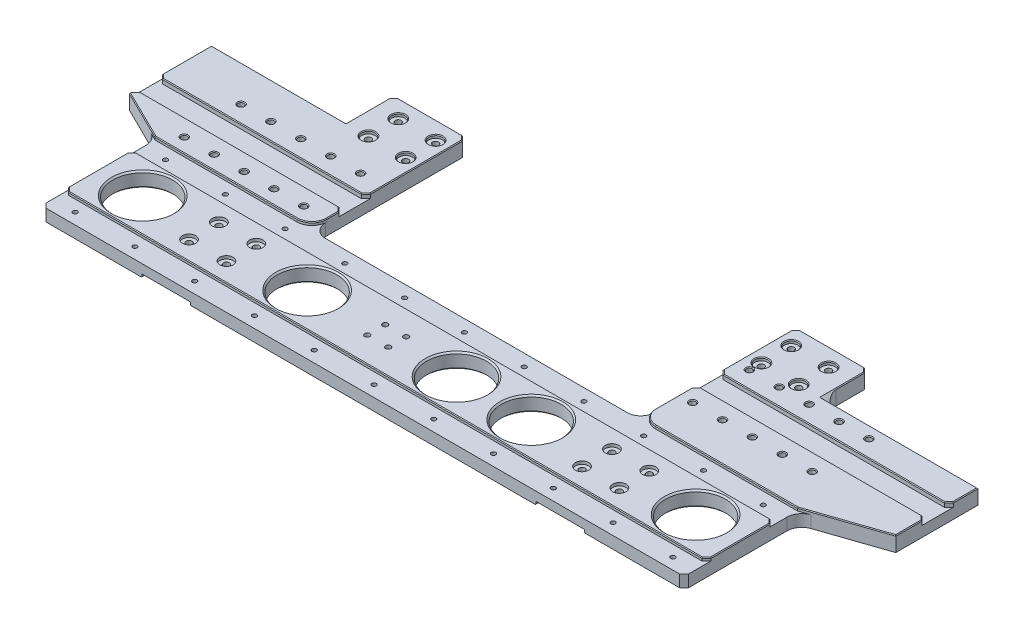
SolidWorks part; units mm, degrees
ref_plane "Front Plane" through (0, 0, 0) normal (0, 0, 1) x (1, 0, 0)
ref_plane "Top Plane" through (0, 0, 0) normal (0, 1, 0) x (1, 0, 0)
ref_plane "Right Plane" through (0, 0, 0) normal (1, 0, 0) x (0, 0, -1)
sketch "Sketch1" plane through (0, 0, 0) normal (0, 1, 0) x (1, 0, 0)
  line L0 (-110, 76) -> (110, 76)
  line L1 (0, -55) -> (0, 55) construction
  line L2 (110, 76) -> (110, 179.75)
  line L3 (110, 179.75) -> (159, 179.75)
  line L4 (159, 179.75) -> (159, 0)
  line L5 (-55, 0) -> (55, 0) construction
  line L6 (159, 0) -> (-159, 0)
  line L7 (-159, 179.75) -> (-159, 0)
  line L8 (-110, 179.75) -> (-159, 179.75)
  line L9 (-110, 76) -> (-110, 179.75)
  line L10 (-139.3864, 37.75) -> (-93.4466, 37.75) construction
  line L11 (-144, 47.75) -> (-119, 27.75) construction
  line L12 (-144, 167.75) -> (-119, 147.75) construction
  line L13 (-115.375, 179) -> (-147.625, 179) construction
  line L14 (-115.375, 179) -> (-115.375, 136.5) construction
  line L15 (-115.375, 136.5) -> (-147.625, 136.5) construction
  line L16 (-147.625, 179) -> (-147.625, 136.5) construction
  line L17 (-115.375, 179) -> (-147.625, 136.5) construction
  line L18 (-115.375, 136.5) -> (-147.625, 179) construction
  line L19 (119, 167.75) -> (144, 147.75) construction
  circle A0 centre (-119, 167.75) radius 2
  circle A1 centre (-144, 167.75) radius 2
  circle A2 centre (-144, 147.75) radius 2
  circle A3 centre (-119, 147.75) radius 2
  circle A4 centre (-119, 27.75) radius 2
  circle A5 centre (-119, 47.75) radius 2
  circle A6 centre (-144, 47.75) radius 2
  circle A7 centre (-144, 27.75) radius 2
  circle A8 centre (144, 167.75) radius 2
  circle A9 centre (119, 167.75) radius 2
  circle A10 centre (144, 147.75) radius 2
  circle A11 centre (119, 147.75) radius 2
  circle A12 centre (144, 27.75) radius 2
  circle A13 centre (144, 47.75) radius 2
  circle A14 centre (119, 47.75) radius 2
  circle A15 centre (119, 27.75) radius 2
  circle A16 centre (-20, 68) radius 2 construction
  circle A17 centre (-60, 68) radius 2 construction
  circle A18 centre (-100, 68) radius 2 construction
  circle A19 centre (-140, 68) radius 2 construction
  circle A20 centre (20, 68) radius 2 construction
  circle A21 centre (60, 68) radius 2 construction
  circle A22 centre (100, 68) radius 2 construction
  circle A23 centre (140, 68) radius 2 construction
  circle A24 centre (140, 7.5) radius 2 construction
  circle A25 centre (100, 7.5) radius 2 construction
  circle A26 centre (60, 7.5) radius 2 construction
  circle A27 centre (20, 7.5) radius 2 construction
  circle A28 centre (-20, 7.5) radius 2 construction
  circle A29 centre (-60, 7.5) radius 2 construction
  circle A30 centre (-100, 7.5) radius 2 construction
  circle A31 centre (-140, 7.5) radius 2 construction
  circle A32 centre (-25, 37.75) radius 20 construction
  circle A33 centre (-75, 37.75) radius 20
  circle A34 centre (75, 37.75) radius 20
  circle A35 centre (25, 37.75) radius 20
  circle A36 centre (-125, 123.55) radius 2
  circle A37 centre (-125, 85.55) radius 2
  circle A38 centre (119, 139.75) radius 2
  circle A39 centre (119, 101.75) radius 2
  point P12 (0, 0)
  point P15 (0, 76)
  point P49 (-131.5, 37.75)
  point P96 (-131.5, 157.75)
  point P103 (131.5, 157.75)
  dimension "D5" = 119
  dimension "D6" = 25
  dimension "D8" = 4
  dimension "D10" = 12
  dimension "D11" = 20
  dimension "D12" = 120
  dimension "D13" = 30.25
  dimension "D16" = 40
  dimension "D2" = 7.5
  dimension "D4" = 8
  dimension "D17" = 40
  dimension "D20" = 50
  dimension "D21" = 15
  dimension "D3" = 9
  dimension "D22" = 56.2
  dimension "D23" = 15
  dimension "D25" = 38
  dimension "D26" = 40
  dimension "D28" = 38
  dimension "D14" = 20
  dimension "D18" = 25
  dimension "D29" = 32.25
  dimension "D30" = 42.5
  dimension "D31" = 263
  dimension "D7" = 2
  dimension "D9" = 2
  dimension "D15" = 4
  dimension "D19" = 2
  dimension "D24" = 2
  dimension "D27" = 2
extrude "Boss-Extrude1" add sketch "Sketch1" along normal mid plane 6 contours L0 L9 L8 L7 L6 L4 L3 L2 A39 A38 A11 A37 A36 A34 A33 A32 A30 A28 A27 A26 A25 A24 A22 A20 A19 A18 A17 A16 A14 A12
sketch "Sketch2" plane through (0, -3, 0) normal (0, 1, 0) x (1, 0, 0)
  line L0 (-159, 179.75) -> (-159, 0) construction
  line L1 (-147.625, 0) -> (-159, 0)
  line L2 (-147.625, 0) -> (-147.625, 179.75)
  line L3 (-147.625, 179.75) -> (-159, 179.75)
  line L4 (-159, 0) -> (-159, 179.75)
  line L5 (-110, 179.75) -> (-159, 179.75) construction
  line L7 (159, 0) -> (-159, 0) construction
  line L8 (-147.625, 179) -> (-147.625, 136.5) construction
extrude "Boss-Extrude2" add sketch "Sketch2" against normal blind 2
sketch "Sketch6" plane through (0, 3, 0) normal (0, 1, 0) x (1, 0, 0)
  line L0 (-55, 0) -> (55, 0) construction
  line L1 (159, 0) -> (215, 0)
  line L2 (159, 0) -> (159, 76)
  line L3 (159, 76) -> (215, 76)
  line L4 (215, 0) -> (215, 76)
  line L5 (159, 179.75) -> (159, 0) construction
  line L6 (-110, 76) -> (110, 76) construction
  line L7 (0, 0) -> (0, 76) construction
  line L9 (-215, 0) -> (-215, 76)
  line L10 (-159, 76) -> (-215, 76)
  line L11 (-159, 0) -> (-159, 76)
  line L12 (-159, 0) -> (-215, 0)
  dimension "D1" = 215
extrude "Boss-Extrude5" add sketch "Sketch6" against normal up to surface (8 mm away) up to face at (-153.3125, -5, -89.875)
sketch "Sketch3" plane through (0, 3, 0) normal (0, 1, 0) x (1, 0, 0)
  line L0 (-159, 179.75) -> (-159, 0) construction
  line L1 (215, 15) -> (-215, 15)
  line L2 (215, 15) -> (215, 60.5)
  line L3 (215, 60.5) -> (-215, 60.5)
  line L4 (-215, 15) -> (-215, 60.5)
  line L5 (159, 179.75) -> (159, 0) construction
  line L6 (110, 179.75) -> (159, 179.75) construction
  line L7 (-110, 76) -> (-110, 179.75) construction
  line L8 (-159, 179.75) -> (-110, 179.75)
  line L9 (-159, 179.75) -> (-159, 76)
  line L10 (-159, 76) -> (-110, 76)
  line L11 (-110, 179.75) -> (-110, 76)
  line L12 (-110, 179.75) -> (-159, 179.75) construction
  line L13 (159, 0) -> (-159, 0) construction
  line L14 (110, 76) -> (110, 179.75) construction
  line L16 (110, 179.75) -> (159, 179.75)
  line L17 (110, 179.75) -> (110, 76)
  line L18 (110, 76) -> (159, 76)
  line L19 (159, 179.75) -> (159, 76)
  line L22 (215, 0) -> (215, 76) construction
  line L23 (-215, 76) -> (-215, 0) construction
  line L24 (-110, 76) -> (110, 76) construction
  line L25 (215, 76) -> (159, 76) construction
  circle A0 centre (-75, 37.75) radius 20
  circle A1 centre (-25, 37.75) radius 20 construction
  circle A2 centre (25, 37.75) radius 20
  circle A3 centre (75, 37.75) radius 20
  circle A4 centre (-75, 37.75) radius 20 construction
  circle A5 centre (-25, 37.75) radius 20 construction
  circle A6 centre (25, 37.75) radius 20 construction
  circle A7 centre (75, 37.75) radius 20 construction
  circle A8 centre (-144, 47.75) radius 4.45
  circle A9 centre (-119, 47.75) radius 4.45
  circle A10 centre (-144, 27.75) radius 4.45
  circle A11 centre (-119, 27.75) radius 4.45
  circle A12 centre (-144, 47.75) radius 2 construction
  circle A13 centre (-144, 167.75) radius 2 construction
  circle A14 centre (-119, 27.75) radius 2 construction
  circle A15 centre (-119, 47.75) radius 2 construction
  circle A16 centre (-144, 27.75) radius 2 construction
  circle A17 centre (119, 47.75) radius 4.45
  circle A18 centre (119, 27.75) radius 4.45
  circle A19 centre (144, 27.75) radius 4.45
  circle A20 centre (144, 47.75) radius 4.45
  circle A21 centre (-144, 167.75) radius 4.45
  circle A22 centre (119, 101.75) radius 2 construction
  circle A23 centre (-119, 167.75) radius 4.45
  circle A24 centre (-144, 147.75) radius 4.45
  circle A25 centre (-125, 123.55) radius 2
  circle A26 centre (-119, 147.75) radius 4.45
  circle A27 centre (-125, 85.55) radius 2
  circle A28 centre (119, 167.75) radius 4.45
  circle A29 centre (119, 139.75) radius 2
  circle A30 centre (119, 147.75) radius 4.45
  circle A31 centre (119, 101.75) radius 2
  circle A32 centre (144, 147.75) radius 4.45
  circle A33 centre (144, 167.75) radius 4.45
  circle A35 centre (-125, 123.55) radius 2 construction
  circle A36 centre (-125, 85.55) radius 2 construction
  circle A37 centre (119, 139.75) radius 2 construction
  dimension "D1" = 8.9
  dimension "D2" = 15
  dimension "D4" = 45.5
extrude "Boss-Extrude3" add sketch "Sketch3" along normal blind 2
sketch "Sketch4" plane through (0, -3, 0) normal (0, -1, 0) x (1, 0, 0)
  line L0 (110, -179.75) -> (110, -76)
  line L1 (110, -76) -> (-110, -76)
  line L2 (-110, -76) -> (-110, -179.75)
  line L3 (-110, -179.75) -> (-115.375, -179.75)
  line L4 (159, 0) -> (-147.625, 0) construction
  line L5 (-110, -76) -> (-110, -179.75) construction
  line L6 (-115.375, -179.75) -> (-115.375, 0)
  line L8 (-115.375, 0) -> (116, 0)
  line L9 (116, 0) -> (116, -179.75)
  line L11 (116, -179.75) -> (110, -179.75)
  line L12 (116, -183.9) -> (116, -131.6) construction
  line L14 (159, 0) -> (148.25, 0)
  line L15 (159, 0) -> (159, -179.75)
  line L16 (159, -179.75) -> (148.25, -179.75)
  line L17 (148.25, 0) -> (148.25, -179.75)
  line L19 (-110, -179.75) -> (-147.625, -179.75) construction
  line L20 (-110, -76) -> (110, -76) construction
  line L21 (110, -76) -> (110, -179.75) construction
  line L22 (110, -179.75) -> (159, -179.75) construction
  line L23 (159, -179.75) -> (159, 0) construction
  line L24 (-115.375, -179) -> (-115.375, -136.5) construction
  line L25 (-115.375, -136.5) -> (-147.625, -136.5) construction
  line L26 (-115.375, -136.5) -> (-147.625, -136.5) construction
  line L27 (0.3125, 0) -> (0.3125, -76.0006) construction
  line L28 (116, -136.5) -> (148.25, -136.5) construction
  circle A8 centre (-100, -68) radius 2
  circle A9 centre (-60, -68) radius 2
  circle A10 centre (-20, -68) radius 2
  circle A11 centre (20, -68) radius 2
  circle A12 centre (60, -68) radius 2
  circle A13 centre (100, -68) radius 2
  circle A14 centre (100, -7.5) radius 2
  circle A15 centre (60, -7.5) radius 2
  circle A16 centre (20, -7.5) radius 2
  circle A17 centre (-20, -7.5) radius 2
  circle A18 centre (-60, -7.5) radius 2
  circle A19 centre (-100, -7.5) radius 2
  circle A20 centre (-100, -7.5) radius 2 construction
  circle A21 centre (-60, -7.5) radius 2 construction
  circle A22 centre (-20, -7.5) radius 2 construction
  circle A23 centre (20, -7.5) radius 2 construction
  circle A24 centre (60, -7.5) radius 2 construction
  circle A25 centre (100, -7.5) radius 2 construction
  circle A26 centre (-100, -68) radius 2 construction
  circle A27 centre (-60, -68) radius 2 construction
  circle A28 centre (-20, -68) radius 2 construction
  circle A29 centre (20, -68) radius 2 construction
  circle A30 centre (60, -68) radius 2 construction
  circle A31 centre (100, -68) radius 2 construction
  circle A32 centre (-75, -37.75) radius 20 construction
  circle A34 centre (25, -37.75) radius 20 construction
  circle A35 centre (75, -37.75) radius 20 construction
  circle A36 centre (-75, -37.75) radius 20
  circle A38 centre (25, -37.75) radius 20
  circle A39 centre (75, -37.75) radius 20
extrude "Boss-Extrude4" add sketch "Sketch4" along normal blind 2
fillet "Fillet1" radius 10 2 edges at (-110, 4, -76) (110, 4, -76)
fillet "Fillet2" radius 9 2 edges at (110, -1, -76) (-110, -1, -76)
sketch "Sketch9" plane through (0, 3, 0) normal (0, 1, 0) x (1, 0, 0)
  line L0 (215, 60.5) -> (-215, 60.5) construction
  line L1 (-215, 76) -> (-215, 60.5) construction
  line L2 (-215, 15) -> (215, 15) construction
  circle A0 centre (-200, 68) radius 1.5
  circle A1 centre (-200, 7.5) radius 1.5
  circle A2 centre (-160, 7.5) radius 1.5
  circle A3 centre (-160, 68) radius 1.5
  circle A4 centre (-120, 7.5) radius 1.5
  circle A5 centre (-120, 68) radius 1.5
  circle A6 centre (-80, 7.5) radius 1.5
  circle A7 centre (-80, 68) radius 1.5
  circle A8 centre (-40, 7.5) radius 1.5
  circle A9 centre (-40, 68) radius 1.5
  circle A10 centre (0, 7.5) radius 1.5
  circle A11 centre (0, 68) radius 1.5
  circle A12 centre (40, 7.5) radius 1.5
  circle A13 centre (40, 68) radius 1.5
  circle A14 centre (80, 7.5) radius 1.5
  circle A15 centre (80, 68) radius 1.5
  circle A16 centre (120, 7.5) radius 1.5
  circle A17 centre (120, 68) radius 1.5
  circle A18 centre (160, 7.5) radius 1.5
  circle A19 centre (160, 68) radius 1.5
  circle A20 centre (200, 7.5) radius 1.5
  circle A21 centre (200, 68) radius 1.5
  dimension "D3" = 3
  dimension "D1" = 7.5
  dimension "D2" = 15
  dimension "D4" = 7.5
  dimension "D6" = 40
  dimension "D5" = 11
extrude "Cut-Extrude2" cut sketch "Sketch9" against normal through all
sketch "Sketch10" plane through (0, 5, 0) normal (0, 1, 0) x (1, 0, 0)
  line L0 (159, 179.75) -> (159, 76) construction
  line L1 (159, 147.75) -> (264, 147.75)
  line L2 (159, 147.75) -> (159, 76)
  line L3 (159, 76) -> (215, 76)
  line L5 (-159, 179.75) -> (-159, 76) construction
  line L6 (-159, 147.75) -> (-249, 147.75)
  line L7 (-159, 147.75) -> (-159, 76)
  line L8 (-159, 76) -> (-215, 76)
  line L10 (-215, 76) -> (-215, 60.5) construction
  line L11 (-159, 76) -> (-215, 76) construction
  line L12 (-249, 147.75) -> (-249, 92.75)
  line L13 (-249, 92.75) -> (-215, 76)
  line L14 (264, 147.75) -> (264, 92.75)
  line L15 (264, 92.75) -> (215, 76)
  circle A0 centre (119, 139.75) radius 2 construction
  dimension "D1" = 8
  dimension "D2" = 55
  dimension "D3" = 90
  dimension "D4" = 105
extrude "Boss-Extrude6" add sketch "Sketch10" against normal up to surface (10 mm away) up to face at (-160, -5, -6)
sketch "Sketch11" plane through (0, 5, 0) normal (0, 1, 0) x (1, 0, 0)
  line L0 (0, 0) -> (0, 210.3149) construction
  line L1 (0, -5.5) -> (0, 5.5) construction
  circle A0 centre (119, 101.75) radius 2 construction
  circle A1 centre (119, 139.75) radius 2 construction
  circle A2 centre (119, 101.75) radius 2
  circle A3 centre (119, 139.75) radius 2
  circle A4 centre (139, 139.75) radius 2
  circle A5 centre (139, 101.75) radius 2
  circle A6 centre (159, 139.75) radius 2
  circle A7 centre (159, 101.75) radius 2
  circle A8 centre (179, 139.75) radius 2
  circle A9 centre (179, 101.75) radius 2
  circle A10 centre (199, 139.75) radius 2
  circle A11 centre (199, 101.75) radius 2
  circle A22 centre (-125, 85.55) radius 2 construction
  circle A23 centre (-125, 123.55) radius 2 construction
  circle A24 centre (-125, 85.55) radius 2
  circle A25 centre (-125, 123.55) radius 2
  circle A26 centre (-145, 123.55) radius 2
  circle A27 centre (-145, 85.55) radius 2
  circle A28 centre (-165, 123.55) radius 2
  circle A29 centre (-165, 85.55) radius 2
  circle A30 centre (-185, 123.55) radius 2
  circle A31 centre (-185, 85.55) radius 2
  circle A32 centre (-205, 123.55) radius 2
  circle A33 centre (-205, 85.55) radius 2
  dimension "D2" = 20
  dimension "D4" = 20
  dimension "D1" = 5
  dimension "D3" = 5
extrude "Cut-Extrude3" cut sketch "Sketch11" against normal through all
sketch "Sketch13" plane through (0, 5, 0) normal (0, 1, 0) x (1, 0, 0)
  line L0 (215, 76) -> (215, 0) construction
  line L1 (0, 0) -> (0, 116.9605) construction
  circle A0 centre (185, 37.75) radius 20
  circle A4 centre (-185, 37.75) radius 20
  circle A6 centre (25, 37.75) radius 20 construction
  circle A7 centre (25, 37.75) radius 20 construction
  point P12 (0, 0)
  dimension "D1" = 40
  dimension "D2" = 30
extrude "Cut-Extrude5" cut sketch "Sketch13" against normal through all
chamfer "Chamfer2" distance 1 angle 45 10 edges at (-75, -5, -57.75) (25, -5, -57.75) (75, -5, -57.75) (75, 5, -17.75) (25, 5, -17.75) (-75, 5, -17.75) (-185, 5, -57.75) (-185, -5, -57.75) (185, 5, -17.75) (185, -5, -17.75)
sketch "Sketch12" plane through (0, 5, 0) normal (0, 1, 0) x (1, 0, 0)
  line L0 (-125, 123.55) -> (-125, 85.55) construction
  line L1 (-125, 104.55) -> (-179.5, 104.55) construction
  line L3 (-249, 97.05) -> (-110, 97.05)
  line L4 (-249, 97.05) -> (-249, 112.05)
  line L5 (-249, 112.05) -> (-110, 112.05)
  line L6 (-110, 97.05) -> (-110, 112.05)
  line L7 (-249, 97.05) -> (-110, 112.05) construction
  line L8 (-249, 112.05) -> (-110, 97.05) construction
  line L11 (-249, 147.75) -> (-249, 92.75) construction
  line L13 (-110, 86) -> (-110, 179.75) construction
  line L14 (119, 139.75) -> (119, 101.75) construction
  line L15 (264, 128.25) -> (110, 128.25)
  line L16 (264, 128.25) -> (264, 113.25)
  line L17 (264, 113.25) -> (110, 113.25)
  line L18 (110, 128.25) -> (110, 113.25)
  line L19 (264, 128.25) -> (110, 113.25) construction
  line L20 (264, 113.25) -> (110, 128.25) construction
  line L21 (119, 120.75) -> (187, 120.75) construction
  line L22 (110, 179.75) -> (110, 86) construction
  line L23 (264, 92.75) -> (264, 147.75) construction
  point P14 (187, 120.75)
  dimension "D1" = 15
  dimension "D2" = 15
extrude "Cut-Extrude4" cut sketch "Sketch12" against normal blind 3
chamfer "Chamfer1" distance 3 angle 45 18 edges at (159, 0, -179.75) (110, 0, -179.75) (-110, 0, -179.75) (-159, 0, -179.75) (-215, -1, 0) (215, -1, 0) (-110, 3.5, -112.05) (-110, 3.5, -97.05) (-215, 4, -15) (215, 4, -15) (215, 4, -60.5) (-215, 4, -60.5) (-249, 3.5, -97.05) (-249, 3.5, -112.05) (264, 3.5, -113.25) (264, 3.5, -128.25) (110, 3.5, -128.25) (110, 3.5, -113.25)
chamfer "Chamfer3" distance 0.5 angle 45 76 edges at (-167.5, 5, -76) (-144, 5, -163.3) (-119, 5, -163.3) (-144, 5, -143.3) (-125, 5, -121.55) (-119, 5, -143.3) (-125, 5, -83.55) (119, 5, -163.3) (119, 5, -137.75) (119, 5, -143.3) (119, 5, -99.75) (144, 5, -143.3) (144, 5, -163.3) (116, -5, -89.875) (-115.375, -5, -89.875) (148.25, -5, -89.875) (-110, 5, -90.025) (-112.9289, 5, -78.9289) (167.5, 5, -76) (112.9289, 5, -78.9289) (159, 5, -162.25) (239.5, 5, -84.375) (264, 5, -101.5) (211.5, 5, -147.75) (-204, 5, -147.75) (-249, 5, -131.4) (-232, 5, -84.375) (-145, 5, -83.55) (199, 5, -137.75) (-185, 5, -83.55) (-165, 5, -121.55) (-165, 5, -83.55) (-145, 5, -121.55) (159, 5, -99.75) (139, 5, -137.75) (139, 5, -99.75) (199, 5, -99.75) (179, 5, -137.75) (179, 5, -99.75) (159, 5, -137.75) (-205, 5, -121.55) (-205, 5, -83.55) (-185, 5, -121.55) (264, 5, -139.5) (187, 5, -113.25) (110, 5, -98.125) (111.5, 5, -111.75) (262.5, 5, -111.75) (187, 5, -128.25) (134.5, 5, -179.75) (110, 5, -154) (111.5, 5, -178.25) (157.5, 5, -178.25) (111.5, 5, -129.75) (262.5, 5, -129.75) (-179.5, 5, -97.05) (-249, 5, -93.4) (-111.5, 5, -95.55) (-247.5, 5, -95.55) (-179.5, 5, -112.05) (-110, 5, -145.9) (-134.5, 5, -179.75) (-159, 5, -162.25) (-157.5, 5, -178.25) (-111.5, 5, -178.25) (-111.5, 5, -113.55) (-247.5, 5, -113.55) (0, 5, -15) (-215, 5, -37.75) (215, 5, -37.75) (0, 5, -60.5) (-213.5, 5, -59) (213.5, 5, -59) (213.5, 5, -16.5) (-213.5, 5, -16.5) (-147.625, -5, -89.875)
fillet "Fillet3" radius 10 4 edges at (159, -0.25, -147.75) (-159, -0.25, -147.75) (-215, -1, -76) (215, -1, -76)
sketch "Sketch14" plane through (0, -5, 0) normal (0, -1, 0) x (1, 0, 0)
  line L0 (115.5, 0) -> (-114.875, 0) construction
  circle A0 centre (-15, -32) radius 1.75
  circle A1 centre (-29, -32) radius 1.75
  circle A2 centre (-29, -44) radius 1.75
  circle A3 centre (-15, -44) radius 1.75
  point P2 (-9.3894, -32.3512)
  point P3 (-15, -32)
  point P4 (0, 0)
  point P14 (-8.5026, -42.25)
  point P15 (0, 0)
  dimension "D6" = 3.5
  dimension "D3" = 15
  dimension "D4" = 14
  dimension "D5" = 12
  dimension "D7" = 32
  dimension "D1" = 2
  dimension "D2" = 2
extrude "Cut-Extrude6" cut sketch "Sketch14" against normal through all
